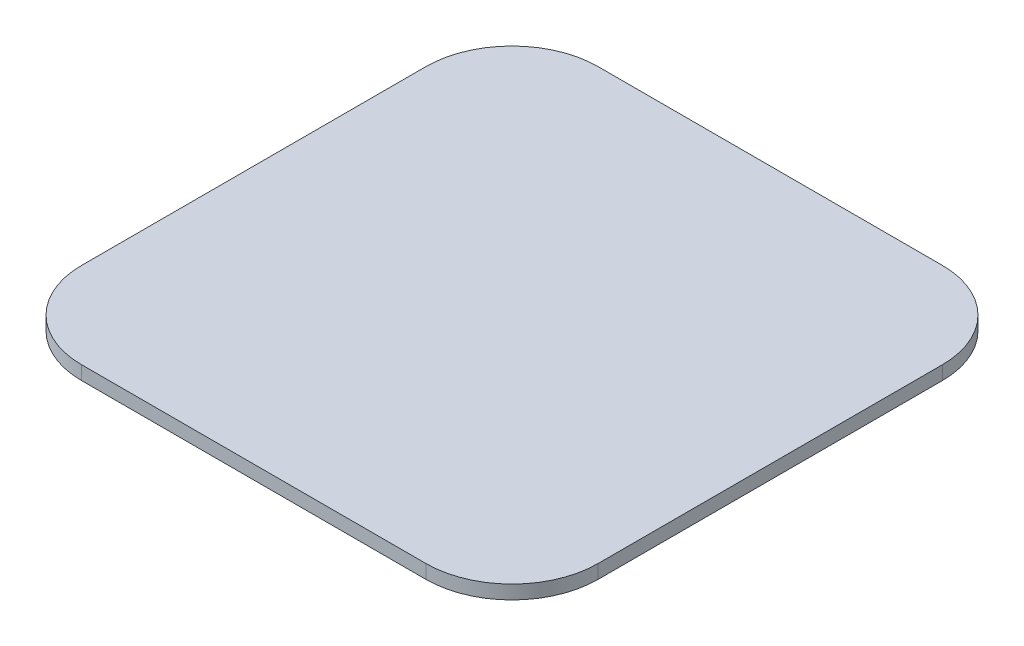
SolidWorks part; units mm, degrees
ref_plane "Front Plane" through (0, 0, 0) normal (0, 0, 1) x (1, 0, 0)
ref_plane "Top Plane" through (0, 0, 0) normal (0, 1, 0) x (1, 0, 0)
ref_plane "Right Plane" through (0, 0, 0) normal (1, 0, 0) x (0, 0, -1)
sketch "Sketch1" plane through (0, 0, 0) normal (0, 1, 0) x (1, 0, 0)
  circle A0 centre (0, 0) radius 5
  dimension "D1" = 10
extrude "Boss-Extrude1" add sketch "Sketch1" along normal blind 0.2
sketch "Sketch2" plane through (0, 0.2, 0) normal (0, 1, 0) x (1, 0, 0)
  line L1 (-7.5, 7.5) -> (7.5, 7.5)
  line L2 (-7.5, 7.5) -> (-7.5, -7.5)
  line L3 (-7.5, -7.5) -> (7.5, -7.5)
  line L4 (7.5, 7.5) -> (7.5, -7.5)
  line L5 (-7.5, 7.5) -> (7.5, -7.5) construction
  line L6 (-7.5, -7.5) -> (7.5, 7.5) construction
  point P0 (0, 0)
  dimension "D1" = 15
  dimension "D2" = 15
extrude "Boss-Extrude2" add sketch "Sketch2" along normal blind 0.4
fillet "Fillet1" radius 2.5 4 edges at (7.5, 0.4, 7.5) (7.5, 0.4, -7.5) (-7.5, 0.4, -7.5) (-7.5, 0.4, 7.5)
